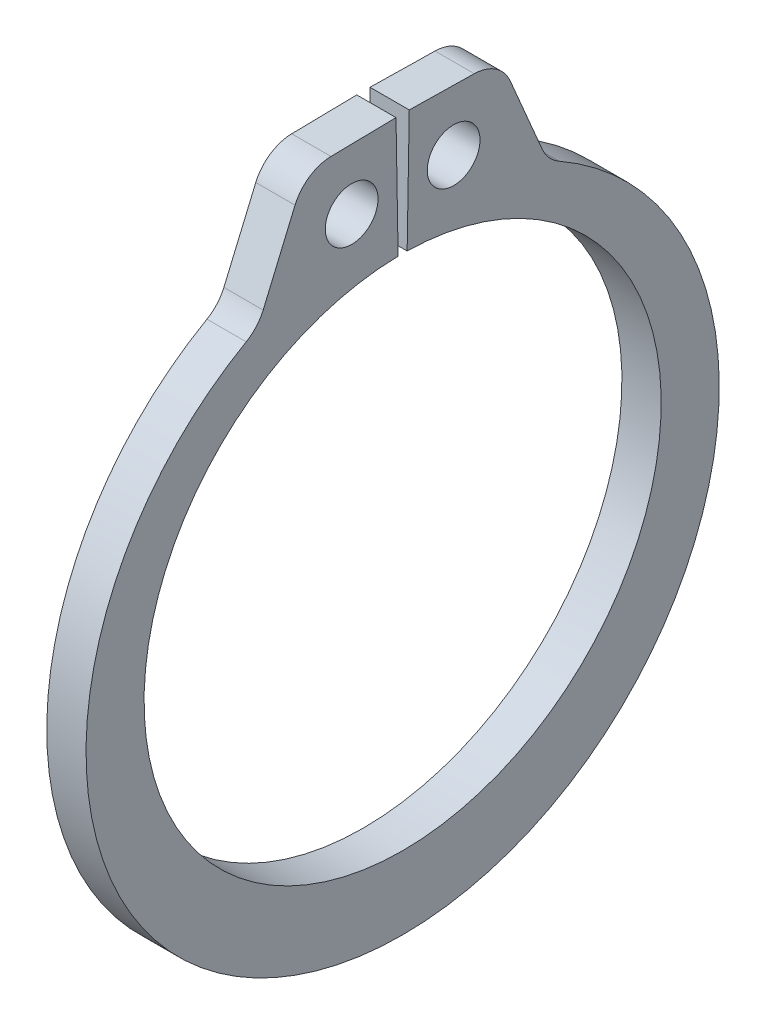
SolidWorks part; units mm, degrees
material "Cast Carbon Steel"
ref_plane "Front" through (0, 0, 0) normal (0, 0, 1) x (1, 0, 0)
ref_plane "Top" through (0, 0, 0) normal (0, 1, 0) x (1, 0, 0)
ref_plane "Right" through (0, 0, 0) normal (1, 0, 0) x (0, 0, -1)
sketch "Sketch1" plane through (0, 0, 0) normal (1, 0, 0) x (0, 0, -1)
  line L0 (0, 0) -> (0, 5.8547) construction
  line L1 (-0.1022, 5.8538) -> (-0.1501, 8.5966)
  line L2 (0.1501, 8.5966) -> (2.2071, 8.5607)
  line L3 (2.2071, 8.5607) -> (3.2813, 6.0365)
  line L4 (0.1022, 5.8538) -> (0.1501, 8.5966)
  line L5 (-0.1501, 8.5966) -> (-2.2071, 8.5607)
  line L6 (-2.2071, 8.5607) -> (-3.2813, 6.0365)
  line L7 (-3.2813, 6.0365) -> (-2.7961, 5.1439) construction
  line L8 (3.2813, 6.0365) -> (2.7961, 5.1439) construction
  line L9 (0, -5.8547) -> (0, -7.5057) construction
  line L10 (-2.2071, 8.5607) -> (-0.1022, 5.8538) construction
  line L11 (0, 5.8547) -> (0, 8.5979) construction
  line L12 (-5.8547, 0) -> (5.8547, 0) construction
  circle A0 centre (0, 0) radius 5.8547 construction
  arc A1 (-0.1022, 5.8538) -> (0.1022, 5.8538) centre (0, 0) ccw
  circle A3 centre (0, 0) radius 9.5885 construction
  circle A4 centre (-1.1547, 7.2072) radius 0.5969
  circle A5 centre (1.1547, 7.2072) radius 0.5969
  arc A6 (-3.2813, 6.0365) -> (3.2813, 6.0365) centre (0, -0.3371) ccw
  point P0 (0, -7.5057)
  dimension "A" = 11.7094
  dimension "Hole" = 1.1938
  dimension "Smin" = 1.016
  dimension "H" = 2.7432
  dimension "D2" = 2.0574
  dimension "Angle" = 1
extrude "Extrude1" add sketch "Sketch1" along normal mid plane 0.889
fillet "Fillet1" radius 0.9017 4 edges at (0, 6.0365, 3.2813) (0, 6.0365, -3.2813) (0, 8.5607, 2.2071) (0, 8.5607, -2.2071)
sketch "Sketch2" plane through (0, 0, 0) normal (0, 0, 1) x (1, 0, 0)
  line L0 (-4.9403, 0) -> (12.8397, 0)
  line L1 (12.8397, 0) -> (12.8397, -6.35)
  line L2 (-0.4953, -6.35) -> (-4.5339, -6.35)
  line L3 (12.8397, -6.35) -> (0.4953, -6.35)
  line L4 (0.4953, -6.35) -> (0.4953, -5.9436)
  line L5 (0.4953, -5.9436) -> (-0.4953, -5.9436)
  line L6 (-0.4953, -5.9436) -> (-0.4953, -6.35)
  line L7 (-0.4953, -6.35) -> (-4.9403, -6.35) construction
  line L8 (-4.9403, -6.35) -> (-4.9403, 0) construction
  line L9 (12.8397, 0) -> (76.391, 0) construction
  line L10 (-4.5339, -6.35) -> (-4.9403, -5.9436)
  line L11 (-4.9403, -5.9436) -> (-4.9403, 0)
  point P10 (0, -5.9436)
  dimension "D2" = 17.78
  dimension "D3" = 4.445
  dimension "D1" = 45
revolve "Revolve1" [suppressed] add sketch "Sketch2" angle 360 about L9
delete or keep bodies "Body-Delete1" [suppressed] type delete bodies bodies 122
equation "\"D2@Sketch2\" = \"D1@Extrude1\"*20"
equation "\"D3@Sketch2\" = \"D2@Sketch2\"/4"
equation "\"D2@Sketch1\" = \"H@Sketch1\"*.75"
